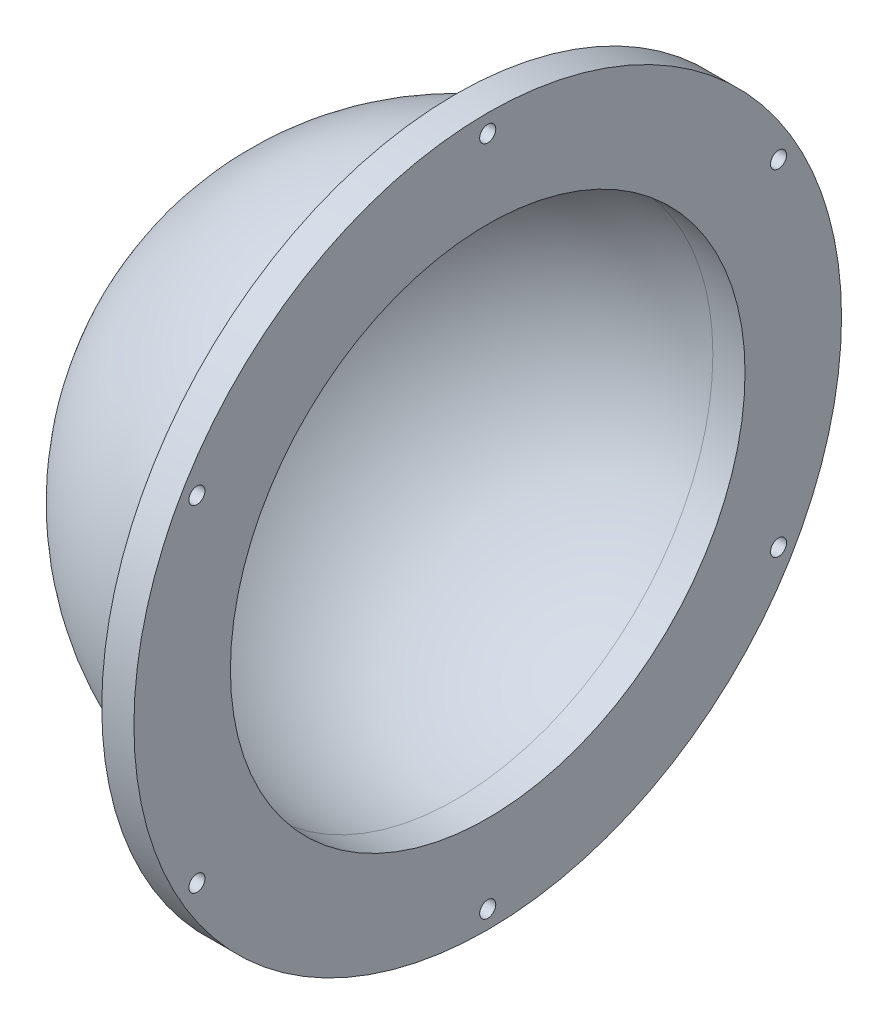
SolidWorks part; units mm, degrees
ref_plane "前视" through (0, 0, 0) normal (0, 0, 1) x (1, 0, 0)
ref_plane "上视" through (0, 0, 0) normal (0, 1, 0) x (1, 0, 0)
ref_plane "右视" through (0, 0, 0) normal (1, 0, 0) x (0, 0, -1)
sketch "草图2" plane through (0, 0, 0) normal (0, 1, 0) x (1, 0, 0)
  line L0 (0, 59.2544) -> (0, -72.2868) construction
  line L1 (95.822, 0) -> (-109.7604, 0) construction
  line L2 (-5, 59.2544) -> (-5, -69.1361) construction
  line L3 (-45, 0) -> (-50, 0)
  line L4 (-5, 45) -> (-5, 55)
  line L5 (-5, 55) -> (0, 55)
  line L6 (0, 55) -> (0, 40)
  line L7 (0, 40) -> (-5, 40)
  arc A0 (-50, 0) -> (-5, 45) centre (-5, 0) cw
  arc A1 (-45, 0) -> (-5, 40) centre (-5, 0) cw
  dimension "D2" = 40
  dimension "D3" = 45
  dimension "D1" = 5
  dimension "D4" = 10
revolve "旋转1" add sketch "草图2" angle 360 about L1
sketch "草图4" plane through (-5, 0, 0) normal (-1, 0, 0) x (0, 0, 1)
  line L0 (0, 66.6161) -> (0, -71.3839) construction
  circle A1 centre (0, 52.2) radius 1.25
  dimension "D1" = 52.2
extrude "切除-拉伸1" cut sketch "草图4" against normal through all
pattern_circular "阵列(圆周)1" count 6 over 360 about axis through (0, 0, 0) along (1, 0, 0) of "切除-拉伸1"
